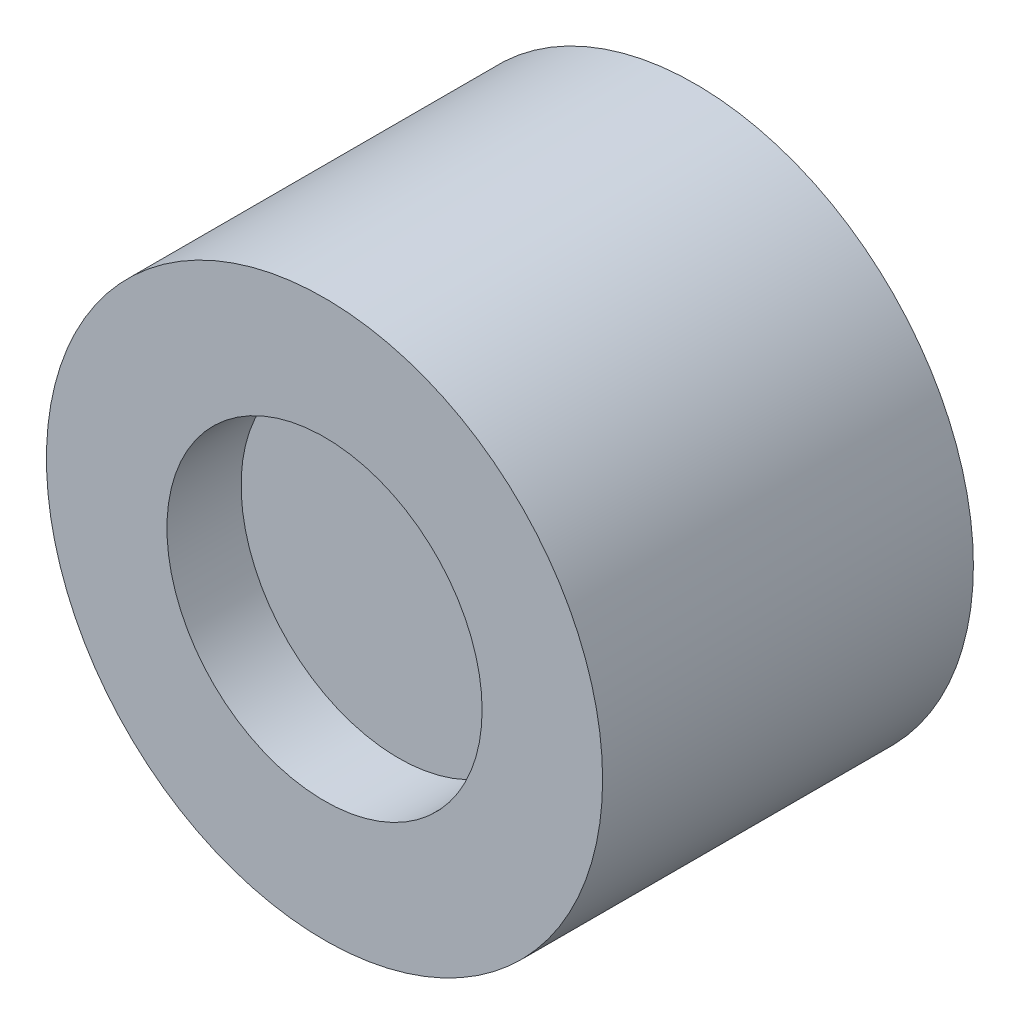
SolidWorks part; units mm, degrees
ref_plane "Alzado" through (0, 0, 0) normal (0, 0, 1) x (1, 0, 0)
ref_plane "Planta" through (0, 0, 0) normal (0, 1, 0) x (1, 0, 0)
ref_plane "Vista lateral" through (0, 0, 0) normal (1, 0, 0) x (0, 0, -1)
sketch "Croquis1" plane through (0, 0, 0) normal (0, 0, 1) x (1, 0, 0)
  circle A0 centre (0, 0) radius 7.5
  dimension "D1" = 15
extrude "Saliente-Extruir1" add sketch "Croquis1" along normal blind 10
sketch "Croquis2" plane through (0, 0, 10) normal (0, 0, 1) x (1, 0, 0)
  circle A0 centre (0, 0) radius 4.25
  dimension "D1" = 8.5
extrude "Cortar-Extruir1" cut sketch "Croquis2" against normal blind 2
